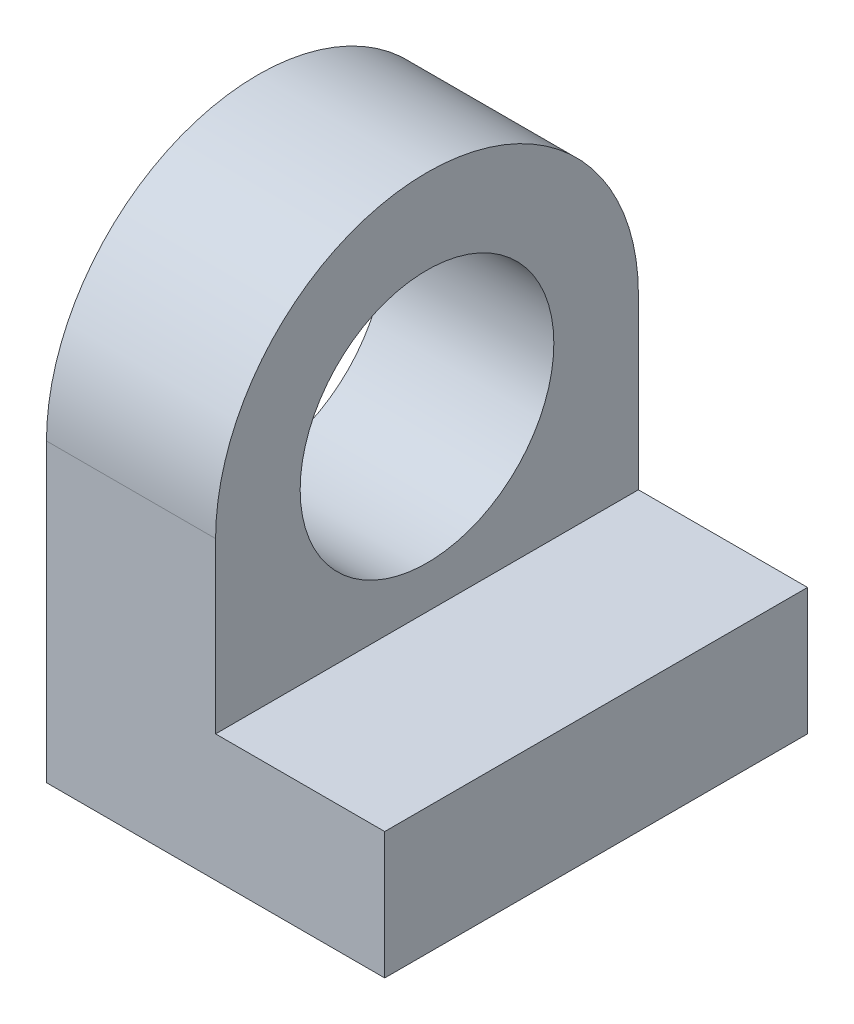
SolidWorks part; units mm, degrees
ref_plane "Alzado" through (0, 0, 0) normal (0, 0, 1) x (1, 0, 0)
ref_plane "Planta" through (0, 0, 0) normal (0, 1, 0) x (1, 0, 0)
ref_plane "Vista lateral" through (0, 0, 0) normal (1, 0, 0) x (0, 0, -1)
sketch "Croquis1" plane through (0, 0, 0) normal (1, 0, 0) x (0, 0, -1)
  line L0 (0, 0) -> (25, 0)
  line L1 (25, 0) -> (25, 17.5)
  line L2 (0, 0) -> (0, 17.5)
  arc A0 (25, 17.5) -> (0, 17.5) centre (12.5, 17.5) ccw
  circle A1 centre (12.5, 17.5) radius 7.5
  dimension "D3" = 15
  dimension "D1" = 25
  dimension "D2" = 17.5
extrude "Saliente-Extruir1" add sketch "Croquis1" against normal blind 20
sketch "Croquis2" plane through (0, 0, 0) normal (0, 0, 1) x (1, 0, 0)
  line L0 (0, 7.5) -> (-10, 7.5)
  line L1 (0, 17.5) -> (0, 0) construction
  line L2 (-10, 7.5) -> (-10, 30)
  line L3 (0, 30) -> (-20, 30) construction
  line L4 (-10, 30) -> (0, 30)
  line L5 (0, 30) -> (0, 7.5)
  line L6 (-20, 0) -> (0, 0) construction
  dimension "D1" = 7.5
  dimension "D2" = 10
extrude "Cortar-Extruir1" cut sketch "Croquis2" against normal up to next
